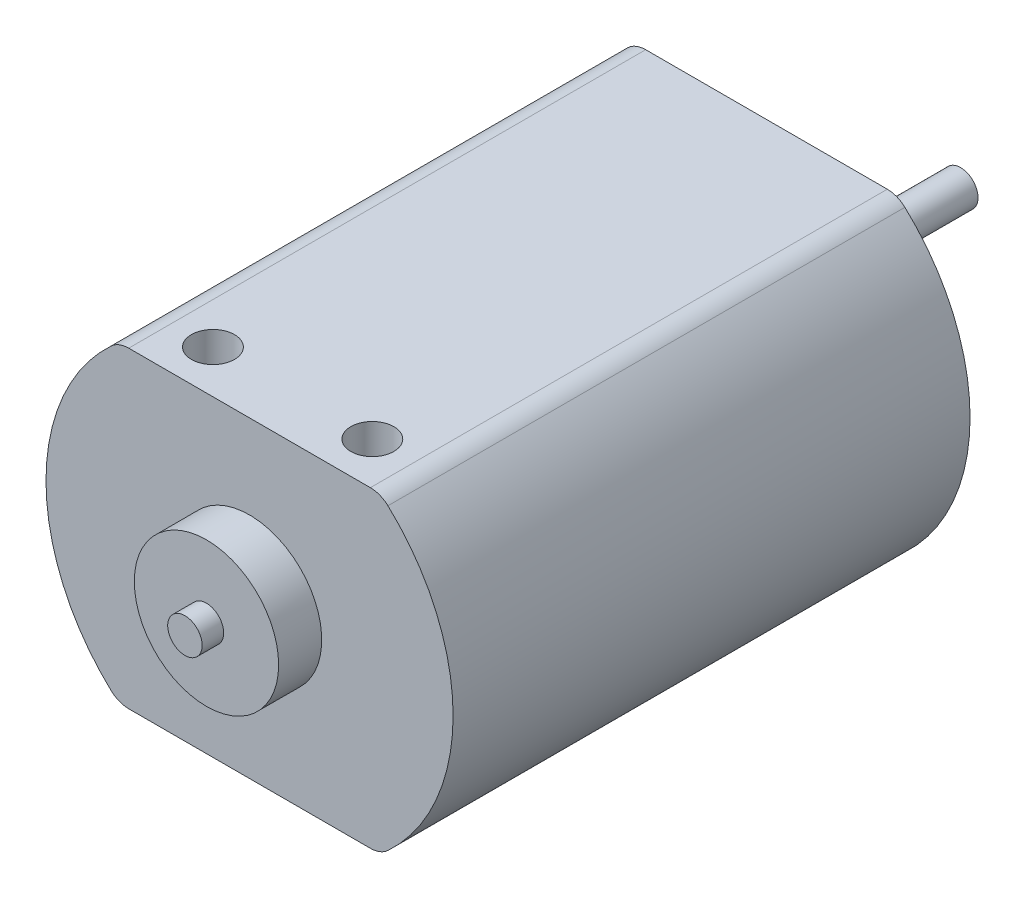
SolidWorks part; units mm, degrees
material "6061 Alloy"
ref_plane "Front Plane" through (0, 0, 0) normal (0, 0, 1) x (1, 0, 0)
ref_plane "Top Plane" through (0, 0, 0) normal (0, 1, 0) x (1, 0, 0)
ref_plane "Right Plane" through (0, 0, 0) normal (1, 0, 0) x (0, 0, -1)
sketch "Sketch1" plane through (0, 0, 0) normal (0, 0, 1) x (1, 0, 0)
  line L1 (-7.1233, -9.2075) -> (7.1233, -9.2075)
  line L3 (-7.1233, 9.2075) -> (7.1233, 9.2075)
  line L5 (-10.7893, -5.2562) -> (10.7893, 5.2562) construction
  line L6 (-10.7893, 5.2562) -> (10.7893, -5.2562) construction
  arc A0 (-8.1595, 8.8011) -> (-8.1595, -8.8011) centre (0, 0) ccw
  arc A1 (8.1595, -8.8011) -> (8.1595, 8.8011) centre (0, 0) ccw
  arc A2 (-7.1233, -9.2075) -> (-8.1595, -8.8011) centre (-7.1233, -7.6835) cw
  arc A3 (7.1233, -9.2075) -> (8.1595, -8.8011) centre (7.1233, -7.6835) ccw
  arc A4 (7.1233, 9.2075) -> (8.1595, 8.8011) centre (7.1233, 7.6835) cw
  arc A5 (-7.1233, 9.2075) -> (-8.1595, 8.8011) centre (-7.1233, 7.6835) ccw
  point P14 (7.6979, -9.2075)
  dimension "D1" = 1.524
  dimension "D2" = 9.2075
  dimension "D4" = 12.0015
  dimension "D3" = 9.2075
extrude "Boss-Extrude1" add sketch "Sketch1" along normal blind 30.48
sketch "Sketch2" plane through (0, 0, 30.48) normal (0, 0, 1) x (1, 0, 0)
  circle A0 centre (0, 0) radius 4.2545
extrude "Boss-Extrude2" add sketch "Sketch2" along normal blind 2.54
sketch "Sketch3" plane through (0, 0, 33.02) normal (0, 0, 1) x (1, 0, 0)
  circle A0 centre (0, 0) radius 1.016
extrude "Boss-Extrude3" add sketch "Sketch3" along normal blind 1.27
sketch "Sketch4" plane through (0, 0, 0) normal (0, 0, -1) x (-1, 0, 0)
  circle A0 centre (0, 0) radius 3.048
extrude "Boss-Extrude4" add sketch "Sketch4" along normal blind 1.5875
sketch "Sketch5" plane through (0, 0, -1.5875) normal (0, 0, -1) x (-1, 0, 0)
  circle A0 centre (0, 0) radius 1.0287
  arc A1 (-8.1595, 8.8011) -> (-8.1595, -8.8011) centre (0, 0) ccw construction
  arc A2 (8.1595, -8.8011) -> (8.1595, 8.8011) centre (0, 0) ccw construction
extrude "Boss-Extrude5" add sketch "Sketch5" along normal blind 9.8552
sketch "Sketch6" plane through (0, 9.2075, 0) normal (0, 1, 0) x (1, 0, 0)
  line L0 (7.1233, -30.48) -> (-7.1233, -30.48) construction
  line L2 (0, -30.48) -> (0, -20.3938) construction
  circle A0 centre (4.699, -27.94) radius 1.27
  circle A1 centre (-4.699, -27.94) radius 1.27
  dimension "D3" = 4.699
  dimension "D2" = 4.699
extrude "Cut-Extrude1" cut sketch "Sketch6" against normal blind 3.175
